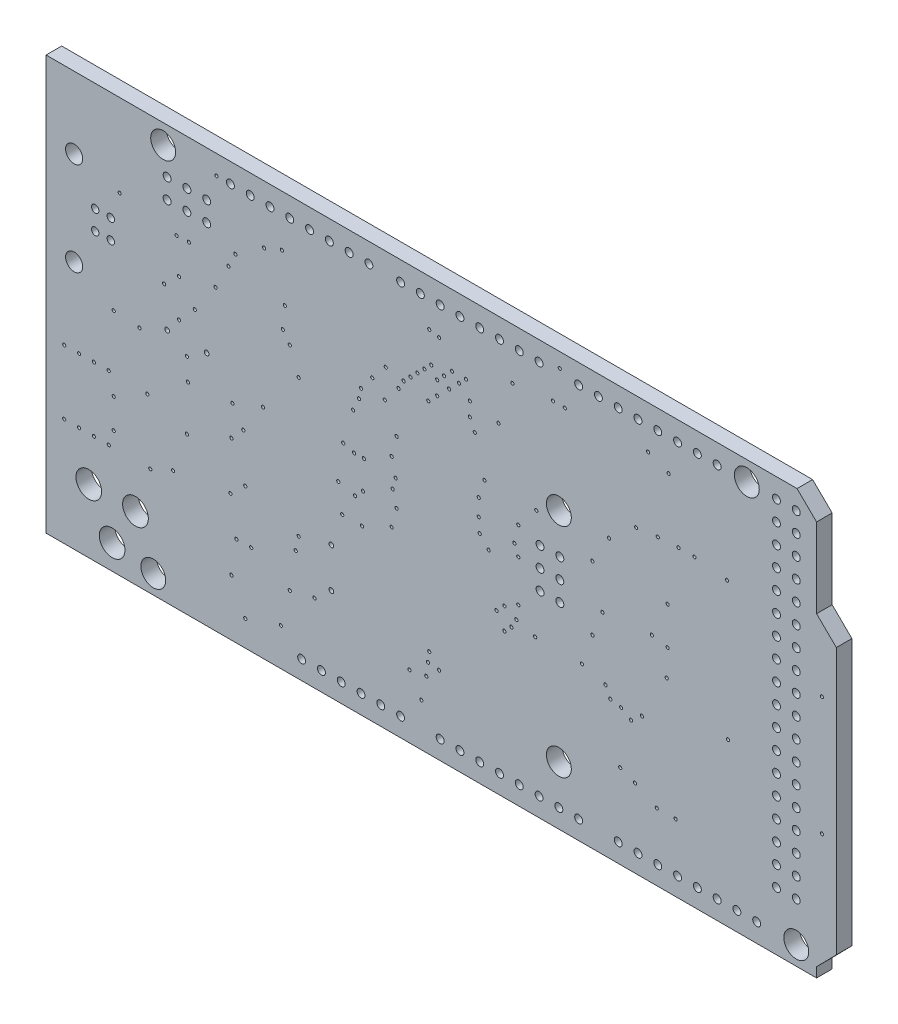
SolidWorks part; units mm, degrees
ref_plane "Front Plane" through (0, 0, 0) normal (0, 0, 1) x (1, 0, 0)
ref_plane "Top Plane" through (0, 0, 0) normal (0, 1, 0) x (1, 0, 0)
ref_plane "Right Plane" through (0, 0, 0) normal (1, 0, 0) x (0, 0, -1)
ref_plane "Plane1" through (0, 0, 0) normal (0, 0, -1) x (-1, 0, 0)
sketch "Sketch1" plane through (0, 0, 0) normal (0, 0, -1) x (-1, 0, 0)
  line L0 (-107.3389, -64.548) -> (27.1822, -64.548)
  line L1 (27.1822, -64.548) -> (27.1822, 7.6333)
  line L2 (27.1822, 7.6333) -> (-107.3389, 7.6333)
  line L3 (-107.3389, 7.6333) -> (-107.3389, -64.548)
  circle A0 centre (-81.88, -46.26) radius 1.6
  circle A1 centre (-0.6, 2) radius 1.6
  circle A2 centre (-75.53, 2) radius 1.6
  circle A3 centre (0.67, -46.26) radius 1.6
  circle A4 centre (-51.4, -13.24) radius 1.6
  circle A5 centre (-51.4, -41.18) radius 1.6
  circle A6 centre (-59.02, -46.26) radius 0.508
  circle A7 centre (-61.56, -46.26) radius 0.508
  circle A8 centre (-64.1, -46.26) radius 0.508
  circle A9 centre (-66.64, -46.26) radius 0.508
  circle A10 centre (-69.18, -46.26) radius 0.508
  circle A11 centre (-71.72, -46.26) radius 0.508
  circle A12 centre (-74.26, -46.26) radius 0.508
  circle A13 centre (-76.8, -46.26) radius 0.508
  circle A14 centre (-36.16, -46.26) radius 0.508
  circle A15 centre (-38.7, -46.26) radius 0.508
  circle A16 centre (-41.24, -46.26) radius 0.508
  circle A17 centre (-43.78, -46.26) radius 0.508
  circle A18 centre (-46.32, -46.26) radius 0.508
  circle A19 centre (-48.86, -46.26) radius 0.508
  circle A20 centre (-51.4, -46.26) radius 0.508
  circle A21 centre (-53.94, -46.26) radius 0.508
  circle A22 centre (-71.72, 2) radius 0.508
  circle A23 centre (-69.18, 2) radius 0.508
  circle A24 centre (-66.64, 2) radius 0.508
  circle A25 centre (-64.1, 2) radius 0.508
  circle A26 centre (-61.56, 2) radius 0.508
  circle A27 centre (-59.02, 2) radius 0.508
  circle A28 centre (-56.48, 2) radius 0.508
  circle A29 centre (-53.94, 2) radius 0.508
  circle A30 centre (-48.987, -18.32) radius 0.508
  circle A31 centre (-51.527, -18.32) radius 0.508
  circle A32 centre (-48.987, -20.86) radius 0.508
  circle A33 centre (-51.527, -20.86) radius 0.508
  circle A34 centre (-48.987, -23.4) radius 0.508
  circle A35 centre (-51.527, -23.4) radius 0.508
  circle A36 centre (-6.188, -1.302) radius 0.508
  circle A37 centre (-6.188, -3.842) radius 0.508
  circle A38 centre (-3.648, -1.302) radius 0.508
  circle A39 centre (-3.648, -3.842) radius 0.508
  circle A40 centre (-1.108, -1.302) radius 0.508
  circle A41 centre (-1.108, -3.842) radius 0.508
  circle A42 centre (-79.34, 2) radius 0.508
  circle A43 centre (-81.88, 2) radius 0.508
  circle A44 centre (-79.34, -41.18) radius 0.508
  circle A45 centre (-81.88, -41.18) radius 0.508
  circle A46 centre (-18.38, -46.26) radius 0.508
  circle A47 centre (-20.92, -46.26) radius 0.508
  circle A48 centre (-23.46, -46.26) radius 0.508
  circle A49 centre (-26, -46.26) radius 0.508
  circle A50 centre (-28.54, -46.26) radius 0.508
  circle A51 centre (-31.08, -46.26) radius 0.508
  circle A52 centre (-27.016, 2) radius 0.508
  circle A53 centre (-24.476, 2) radius 0.508
  circle A54 centre (-21.936, 2) radius 0.508
  circle A55 centre (-19.396, 2) radius 0.508
  circle A56 centre (-16.856, 2) radius 0.508
  circle A57 centre (-14.316, 2) radius 0.508
  circle A58 centre (-11.776, 2) radius 0.508
  circle A59 centre (-9.236, 2) radius 0.508
  circle A60 centre (-48.86, 2) radius 0.508
  circle A61 centre (-46.32, 2) radius 0.508
  circle A62 centre (-43.78, 2) radius 0.508
  circle A63 centre (-41.24, 2) radius 0.508
  circle A64 centre (-38.7, 2) radius 0.508
  circle A65 centre (-36.16, 2) radius 0.508
  circle A66 centre (-33.62, 2) radius 0.508
  circle A67 centre (-31.08, 2) radius 0.508
  circle A68 centre (-6.188, -18.32) radius 0.3048
  circle A69 centre (-1.108, -18.32) radius 0.3048
  circle A70 centre (-22.19, -31.655) radius 0.3048
  circle A71 centre (-22.19, -36.735) radius 0.3048
  circle A72 centre (5.9532, -45.498) radius 1.651
  circle A73 centre (2.956, -40.4942) radius 1.651
  circle A74 centre (8.9504, -40.4942) radius 1.651
  circle A75 centre (6.12, -11.95) radius 0.475
  circle A76 centre (6.12, -9.45) radius 0.475
  circle A77 centre (8.12, -9.45) radius 0.475
  circle A78 centre (8.12, -11.95) radius 0.475
  circle A79 centre (10.83, -4.7) radius 1.1
  circle A80 centre (10.83, -16.7) radius 1.1
  circle A81 centre (-81.88, -18.32) radius 0.508
  circle A82 centre (-79.34, -18.32) radius 0.508
  circle A83 centre (-81.88, -15.78) radius 0.508
  circle A84 centre (-79.34, -15.78) radius 0.508
  circle A85 centre (-81.88, -13.24) radius 0.508
  circle A86 centre (-79.34, -13.24) radius 0.508
  circle A87 centre (-81.88, -10.7) radius 0.508
  circle A88 centre (-79.34, -10.7) radius 0.508
  circle A89 centre (-81.88, -8.16) radius 0.508
  circle A90 centre (-79.34, -8.16) radius 0.508
  circle A91 centre (-81.88, -5.62) radius 0.508
  circle A92 centre (-79.34, -5.62) radius 0.508
  circle A93 centre (-81.88, -3.08) radius 0.508
  circle A94 centre (-79.34, -3.08) radius 0.508
  circle A95 centre (-81.88, -0.54) radius 0.508
  circle A96 centre (-79.34, -0.54) radius 0.508
  circle A97 centre (-81.88, -38.64) radius 0.508
  circle A98 centre (-79.34, -38.64) radius 0.508
  circle A99 centre (-81.88, -36.1) radius 0.508
  circle A100 centre (-79.34, -36.1) radius 0.508
  circle A101 centre (-81.88, -33.56) radius 0.508
  circle A102 centre (-79.34, -33.56) radius 0.508
  circle A103 centre (-81.88, -31.02) radius 0.508
  circle A104 centre (-79.34, -31.02) radius 0.508
  circle A105 centre (-81.88, -28.48) radius 0.508
  circle A106 centre (-79.34, -28.48) radius 0.508
  circle A107 centre (-81.88, -25.94) radius 0.508
  circle A108 centre (-79.34, -25.94) radius 0.508
  circle A109 centre (-81.88, -23.4) radius 0.508
  circle A110 centre (-79.34, -23.4) radius 0.508
  circle A111 centre (-81.88, -20.86) radius 0.508
  circle A112 centre (-79.34, -20.86) radius 0.508
  circle A113 centre (-20.031, -38.64) radius 0.2032
  circle A114 centre (-9.363, -26.194) radius 0.2032
  circle A115 centre (-15.713, -43.847) radius 0.2032
  circle A116 centre (-17.618, -34.576) radius 0.2032
  circle A117 centre (-68.799, -9.684) radius 0.2032
  circle A118 centre (-41.8496, -14.637) radius 0.2032
  circle A119 centre (-48.5044, -14.6624) radius 0.2032
  circle A120 centre (-42.383, -22.13) radius 0.2032
  circle A121 centre (-29.937, -17.939) radius 0.2032
  circle A122 centre (-29.048, -12.097) radius 0.2032
  circle A123 centre (8.29, -26.575) radius 0.2032
  circle A124 centre (5.75, -19.59) radius 0.2032
  circle A125 centre (10.195, -26.575) radius 0.2032
  circle A126 centre (6.385, -26.575) radius 0.2032
  circle A127 centre (12.1, -26.575) radius 0.2032
  circle A128 centre (5.75, -29.115) radius 0.2032
  circle A129 centre (12.1, -34.83) radius 0.2032
  circle A130 centre (8.29, -34.83) radius 0.2032
  circle A131 centre (10.195, -34.83) radius 0.2032
  circle A132 centre (5.75, -32.925) radius 0.2032
  circle A133 centre (6.385, -34.83) radius 0.2032
  circle A134 centre (-0.727, -13.367) radius 0.2032
  circle A135 centre (-4.664, -14.256) radius 0.2032
  circle A136 centre (-13.427, -20.733) radius 0.2032
  circle A137 centre (-8.982, -7.271) radius 0.2032
  circle A138 centre (-9.236, -32.417) radius 0.2032
  circle A139 centre (-30.826, -9.938) radius 0.2032
  circle A140 centre (-31.461, -8.795) radius 0.2032
  circle A141 centre (-32.35, -7.906) radius 0.2032
  circle A142 centre (-33.239, -7.017) radius 0.2032
  circle A143 centre (-34.128, -6.128) radius 0.2032
  circle A144 centre (-35.017, -5.239) radius 0.2032
  circle A145 centre (-34.636, -9.43) radius 0.2032
  circle A146 centre (-35.779, -6.509) radius 0.2032
  circle A147 centre (-35.779, -8.287) radius 0.2032
  circle A148 centre (-36.668, -5.62) radius 0.2032
  circle A149 centre (-37.303, -6.763) radius 0.2032
  circle A150 centre (-37.684, -4.604) radius 0.2032
  circle A151 centre (-38.573, -5.493) radius 0.2032
  circle A152 centre (-39.462, -4.604) radius 0.2032
  circle A153 centre (-39.97, -6.763) radius 0.2032
  circle A154 centre (-39.97, -8.541) radius 0.2032
  circle A155 centre (-27.4478, -10.446) radius 0.2032
  circle A156 centre (-13.554, -2.953) radius 0.2032
  circle A157 centre (-11.141, -30.639) radius 0.2032
  circle A158 centre (-7.331, -10.446) radius 0.2032
  circle A159 centre (-3.775, -22.765) radius 0.2032
  circle A160 centre (-41.24, -20.86) radius 0.2032
  circle A161 centre (-46.193, -17.431) radius 0.2032
  circle A162 centre (-54.36, -28.8) radius 0.2032
  circle A163 centre (-23.587, -27.591) radius 0.2032
  circle A164 centre (-30.445, -20.098) radius 0.2032
  circle A165 centre (-30.572, -15.399) radius 0.2032
  circle A166 centre (-40.605, -9.938) radius 0.2032
  circle A167 centre (-17.999, -15.145) radius 0.2032
  circle A168 centre (-23.714, -19.574) radius 0.2032
  circle A169 centre (-72.99, -10.192) radius 0.2032
  circle A170 centre (-73.117, -27.845) radius 0.2032
  circle A171 centre (-57.8516, -13.0876) radius 0.2032
  circle A172 centre (-9.998, -37.116) radius 0.2032
  circle A173 centre (1.051, -34.83) radius 0.2032
  circle A174 centre (-17.999, -32.798) radius 0.2032
  circle A175 centre (-26.127, -27.591) radius 0.2032
  circle A176 centre (-2.632, -11.589) radius 0.2032
  circle A177 centre (-3.902, -7.144) radius 0.2032
  circle A178 centre (-10.887, -24.543) radius 0.2032
  circle A179 centre (-43.653, -7.398) radius 0.2032
  circle A180 centre (-62.8554, -0.9972) radius 0.2032
  circle A181 centre (-29.175, -8.414) radius 0.2032
  circle A182 centre (-30.064, -21.495) radius 0.2032
  circle A183 centre (-33.747, -43.133) radius 0.2032
  circle A184 centre (-11.141, -45.371) radius 0.2032
  circle A185 centre (1.432, -26.702) radius 0.2032
  circle A186 centre (-9.49, -22.257) radius 0.2032
  circle A187 centre (-9.871, -5.493) radius 0.2032
  circle A188 centre (-46.193, -20.987) radius 0.2032
  circle A189 centre (-43.399, -28.353) radius 0.2032
  circle A190 centre (2.448, -19.844) radius 0.2032
  circle A191 centre (-23.079, -24.162) radius 0.2032
  circle A192 centre (-63.338, -21.114) radius 0.2032
  circle A193 centre (-62.068, -30.758) radius 0.2032
  circle A194 centre (-85.166, -17.05) radius 0.2032
  circle A195 centre (-65.243, -24.924) radius 0.2032
  circle A196 centre (-55.718, -24.924) radius 0.2032
  circle A197 centre (-56.988, -21.749) radius 0.2032
  circle A198 centre (-3.648, -19.971) radius 0.2032
  circle A199 centre (-55.7016, -16.7026) radius 0.2032
  circle A200 centre (-48.36, -28.8) radius 0.2032
  circle A201 centre (-2.632, -16.415) radius 0.2032
  circle A202 centre (-85.166, -32.29) radius 0.2032
  circle A203 centre (-51.511, 2.635) radius 0.2032
  circle A204 centre (-7.442, 2) radius 0.2032
  circle A205 centre (-3.648, -28.607) radius 0.2032
  circle A206 centre (-61.322, -10.176) radius 0.2032
  circle A207 centre (-65.497, -2.064) radius 0.2032
  circle A208 centre (-45.431, -2.064) radius 0.2032
  circle A209 centre (-15.84, -2.064) radius 0.2032
  circle A210 centre (-30.572, -23.4) radius 0.2032
  circle A211 centre (-34.763, -37.243) radius 0.2032
  circle A212 centre (-59.274, -37.878) radius 0.2032
  circle A213 centre (-26.254, -23.654) radius 0.2032
  circle A214 centre (-34.59, -38.513) radius 0.2032
  circle A215 centre (-25.238, -24.67) radius 0.2032
  circle A216 centre (-36.033, -38.675) radius 0.2032
  circle A217 centre (-61.179, -38.64) radius 0.2032
  circle A218 centre (-29.937, -25.813) radius 0.2032
  circle A219 centre (-34.382, -40.164) radius 0.2032
  circle A220 centre (-66.386, -40.037) radius 0.2032
  circle A221 centre (-16.221, -8.033) radius 0.2032
  circle A222 centre (-15.967, -10.827) radius 0.2032
  circle A223 centre (-26, -12.351) radius 0.2032
  circle A224 centre (-25.746, -13.621) radius 0.2032
  circle A225 centre (-24.984, -15.272) radius 0.2032
  circle A226 centre (-16.856, -12.097) radius 0.2032
  circle A227 centre (-34.763, -1.429) radius 0.2032
  circle A228 centre (-44.415, -27.337) radius 0.2032
  circle A229 centre (-44.415, -30.131) radius 0.2032
  circle A230 centre (-46.193, -26.321) radius 0.2032
  circle A231 centre (-45.304, -29.242) radius 0.2032
  circle A232 centre (-45.939, -28.099) radius 0.2032
  circle A233 centre (-45.685, -19.717) radius 0.2032
  circle A234 centre (-36.033, -1.683) radius 0.2032
  circle A235 centre (-11.903, -37.116) radius 0.2032
  circle A236 centre (-63.973, -40.037) radius 0.2032
  circle A237 centre (-32.215, -40.537) radius 0.2032
  circle A238 centre (-16.856, -39.402) radius 0.2032
  circle A239 centre (-65.37, -21.495) radius 0.2032
  circle A240 centre (-65.37, -16.669) radius 0.2032
  circle A241 centre (-2.3145, -7.2075) radius 0.2032
  circle A242 centre (-1.87, -33.56) radius 0.2032
  circle A243 centre (-58.004, -30.893) radius 0.2032
  circle A244 centre (-26.381, -19.971) radius 0.2032
  circle A245 centre (-52.162, -1.429) radius 0.2032
  circle A246 centre (-41.113, -19.082) radius 0.2032
  circle A247 centre (-66.767, -9.684) radius 0.2032
  circle A248 centre (-60.671, -31.909) radius 0.2032
  circle A249 centre (-59.401, -31.147) radius 0.2032
  circle A250 centre (-64.1, -9.811) radius 0.2032
  circle A251 centre (-57.369, -29.623) radius 0.2032
  circle A252 centre (-25.111, -19.971) radius 0.2032
  circle A253 centre (-50.638, -1.429) radius 0.2032
  circle A254 centre (-41.113, -16.923) radius 0.2032
  circle A255 centre (4.988, -6.128) radius 0.2032
  circle A256 centre (-9.363, -41.434) radius 0.2032
extrude "Boss-Extrude1" add sketch "Sketch1" against normal blind 2
sketch "Sketch2" plane through (0, 0, 2) normal (0, 0, 1) x (1, 0, 0)
  line L0 (-14.4311, 4.4986) -> (81.979, 4.4986)
  line L1 (81.979, 4.4986) -> (84.4864, 2.039)
  line L2 (84.4864, 2.039) -> (84.4864, -8.1643)
  line L3 (84.4864, -8.1643) -> (87.0239, -10.6535)
  line L4 (87.0239, -10.6535) -> (87.0239, -44.8195)
  line L5 (87.0239, -44.8195) -> (84.4864, -47.4064)
  line L6 (84.4864, -47.4064) -> (84.4864, -48.6661)
  line L7 (84.4864, -48.6661) -> (-14.4311, -48.6661)
  line L8 (-14.4311, -48.6661) -> (-14.4311, 4.4986)
  line L10 (-44.2888, 20.6195) -> (117.8439, 20.6195)
  line L11 (-44.2888, 20.6195) -> (-44.2888, -69.5248)
  line L12 (-44.2888, -69.5248) -> (117.8439, -69.5248)
  line L13 (117.8439, 20.6195) -> (117.8439, -69.5248)
extrude "Cut-Extrude1" cut sketch "Sketch2" against normal blind 10
